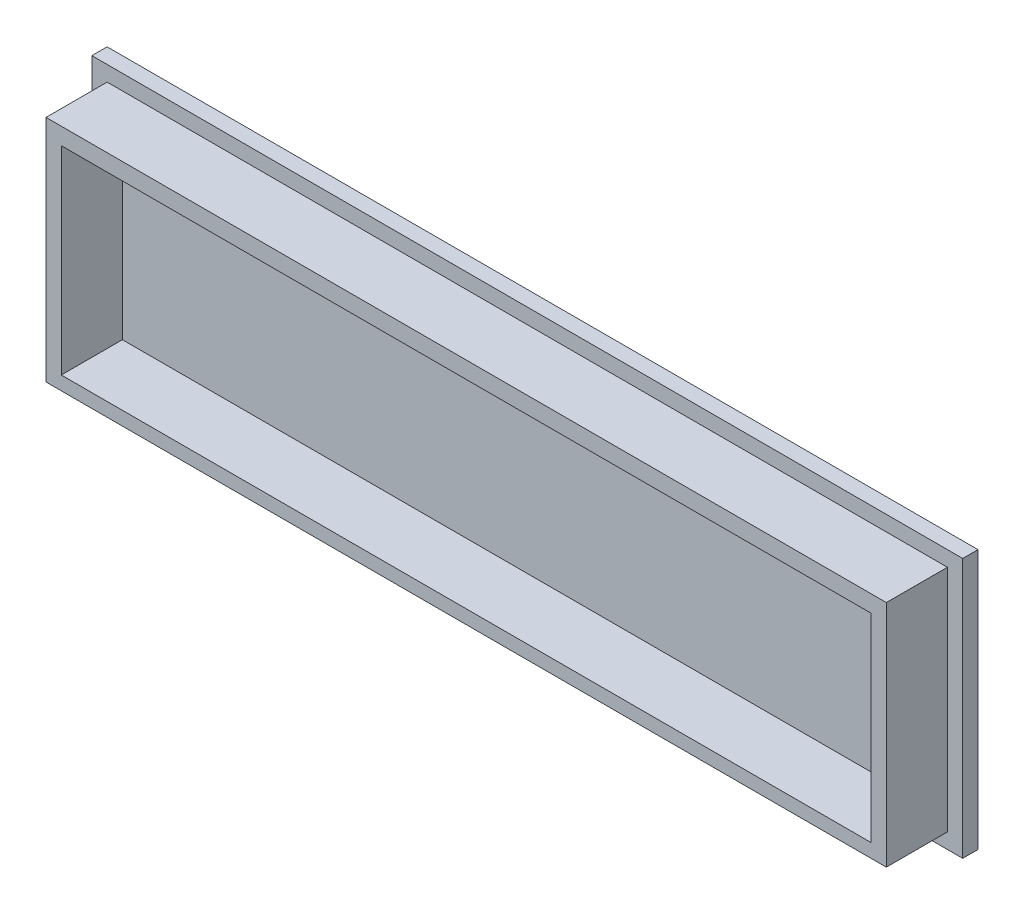
SolidWorks part; units mm, degrees
ref_plane "Front Plane" through (0, 0, 0) normal (0, 0, 1) x (1, 0, 0)
ref_plane "Top Plane" through (0, 0, 0) normal (0, 1, 0) x (1, 0, 0)
ref_plane "Right Plane" through (0, 0, 0) normal (1, 0, 0) x (0, 0, -1)
sketch "Sketch1" plane through (0, 0, 0) normal (0, 0, 1) x (1, 0, 0)
  line L1 (-139.0122, 10.5114) -> (145.9878, 10.5114)
  line L2 (-139.0122, 10.5114) -> (-139.0122, -74.4886)
  line L3 (-139.0122, -74.4886) -> (145.9878, -74.4886)
  line L4 (145.9878, 10.5114) -> (145.9878, -74.4886)
  dimension "D1" = 285
  dimension "D2" = 85
extrude "Boss-Extrude1" add sketch "Sketch1" along normal blind 5
sketch "Sketch2" plane through (0, 0, 5) normal (0, 0, 1) x (1, 0, 0)
  line L0 (-139.0122, 10.5114) -> (-139.0122, -74.4886) construction
  line L1 (-134.0122, 5.5114) -> (140.9878, 5.5114)
  line L2 (-134.0122, 5.5114) -> (-134.0122, -69.4886)
  line L3 (-134.0122, -69.4886) -> (140.9878, -69.4886)
  line L4 (140.9878, 5.5114) -> (140.9878, -69.4886)
  line L5 (145.9878, 10.5114) -> (-139.0122, 10.5114) construction
  line L6 (145.9878, -74.4886) -> (145.9878, 10.5114) construction
  line L7 (-139.0122, -74.4886) -> (145.9878, -74.4886) construction
  dimension "D1" = 5
  dimension "D2" = 5
  dimension "D3" = 5
  dimension "D4" = 5
  dimension "D5" = 275
  dimension "D6" = 75
extrude "Boss-Extrude2" add sketch "Sketch2" along normal blind 20
sketch "Sketch3" plane through (0, 0, 25) normal (0, 0, 1) x (1, 0, 0)
  line L0 (140.9878, -69.4886) -> (140.9878, 5.5114) construction
  line L1 (-129.0122, 0) -> (135.9878, 0)
  line L2 (-129.0122, 0) -> (-129.0122, -65)
  line L3 (-129.0122, -65) -> (135.9878, -65)
  line L4 (135.9878, 0) -> (135.9878, -65)
  line L5 (-134.0122, 5.5114) -> (-134.0122, -69.4886) construction
  dimension "D1" = 265
  dimension "D2" = 5
  dimension "D3" = 5
  dimension "D4" = 65
  dimension "D5" = 65
extrude "Cut-Extrude1" cut sketch "Sketch3" against normal blind 20
